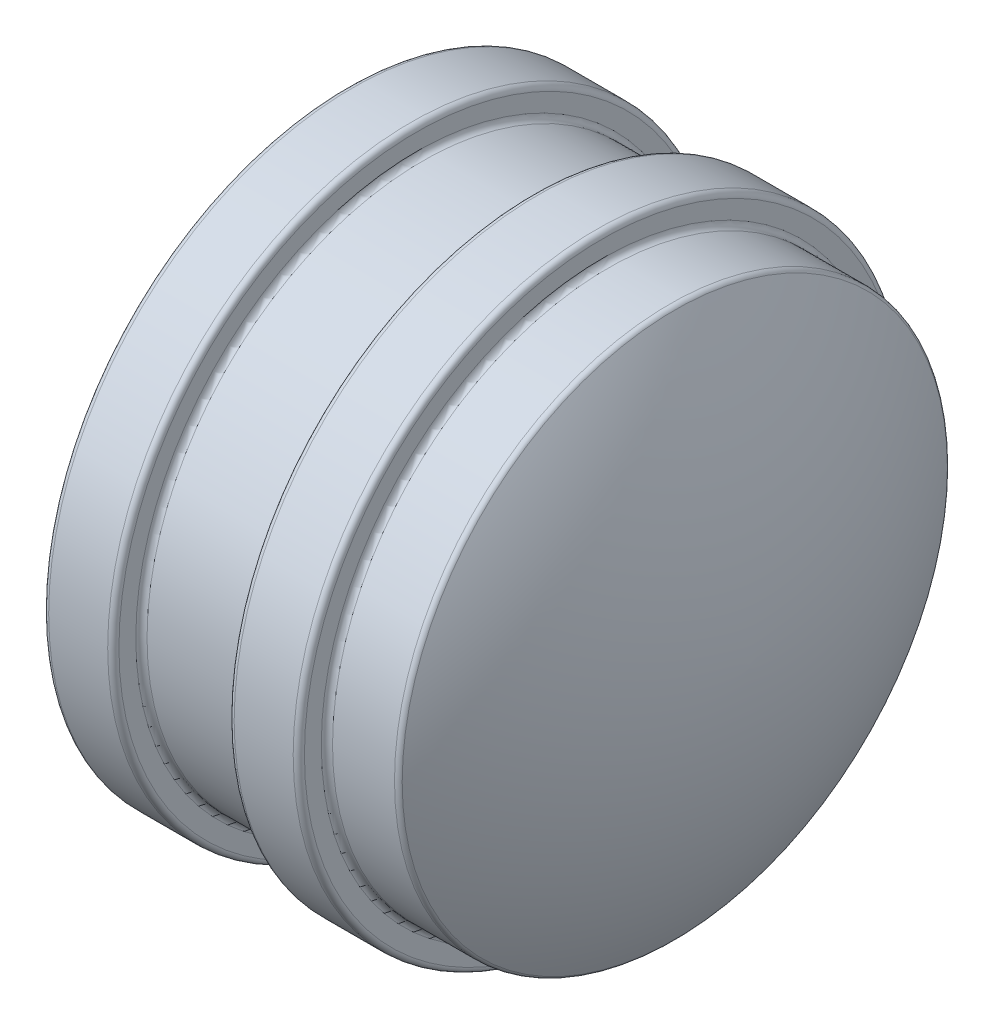
SolidWorks part; units mm, degrees
material "ABS"
ref_plane "Front Plane" through (0, 0, 0) normal (0, 0, 1) x (1, 0, 0)
ref_plane "Top Plane" through (0, 0, 0) normal (0, 1, 0) x (1, 0, 0)
ref_plane "Right Plane" through (0, 0, 0) normal (1, 0, 0) x (0, 0, -1)
sketch "Sketch2" plane through (0, 0, 0) normal (0, 0, 1) x (1, 0, 0)
  line L0 (0, 0) -> (18.1864, 0)
  line L1 (55, 0) -> (-55, 0) construction
  line L2 (14.7574, 0) -> (14.7574, 12.446) construction
  line L3 (14.7574, 12.446) -> (11.557, 12.446)
  line L4 (11.557, 12.446) -> (11.557, 13.716)
  line L5 (11.557, 13.716) -> (8.382, 13.716)
  line L6 (8.382, 13.716) -> (8.382, 12.446)
  line L7 (8.382, 12.446) -> (3.175, 12.446)
  line L8 (3.175, 12.446) -> (3.175, 13.716)
  line L9 (3.175, 13.716) -> (0, 13.716)
  line L10 (0, -55) -> (0, 55) construction
  line L11 (0, 13.716) -> (0, 0)
  arc A0 (14.7574, 12.446) -> (18.1864, 0) centre (-7.2118, -0.3021) cw
  dimension "D7" = 25.4
  dimension "D1" = 5.207
  dimension "D2" = 3.2004
  dimension "D3" = 12.446
  dimension "D4" = 1.27
  dimension "D5" = 18.1864
  dimension "D6" = 3.175
revolve "Revolve1" add sketch "Sketch2" angle 360 about L0
fillet "Fillet1" radius 0.254 8 edges at (14.7574, 0, 12.446) (11.557, 0, 12.446) (11.557, 0, 13.716) (8.382, 0, 13.716) (8.382, 0, 12.446) (3.175, 0, 12.446) (3.175, 0, 13.716) (0, 0, 13.716)
sketch "Sketch3" plane through (0, 0, 0) normal (-1, 0, 0) x (0, 0, 1)
  line L0 (-5.0289, 5.0289) -> (-5.0289, -5.0289) construction
  line L1 (0, 7.112) -> (0, -7.112) construction
  line L2 (5.0289, 5.0289) -> (5.0289, -5.0289) construction
  line L3 (-5.0289, 5.0289) -> (5.0289, 5.0289) construction
  line L4 (-7.112, 0) -> (7.112, 0) construction
  line L5 (-5.0289, -5.0289) -> (5.0289, -5.0289) construction
  circle A0 centre (0, 0) radius 2.54
  circle A1 centre (0, 7.112) radius 2.286
  circle A2 centre (5.0289, 5.0289) radius 2.286
  circle A3 centre (7.112, 0) radius 2.286
  circle A4 centre (5.0289, -5.0289) radius 2.286
  circle A5 centre (0, -7.112) radius 2.286
  circle A6 centre (-5.0289, -5.0289) radius 2.286
  circle A7 centre (-7.112, 0) radius 2.286
  circle A8 centre (-5.0289, 5.0289) radius 2.286
  dimension "D1" = 5.08
  dimension "D2" = 4.572
  dimension "D3" = 7.112
  dimension "D5" = 45
  dimension "D4" = 8
extrude "Cut-Extrude1" cut sketch "Sketch3" against normal blind 6.35
fillet "Fillet2" radius 1.27 9 edges at (6.35, -7.112, 2.286) (6.35, -5.0289, 7.3149) (6.35, 0, 9.398) (6.35, 5.0289, 7.3149) (6.35, 0, 2.54) (6.35, -5.0289, -2.7429) (6.35, 0, -4.826) (6.35, 7.112, 2.286) (6.35, 5.0289, -2.7429)
fillet "Fillet3" radius 0.254 9 edges at (0, -7.112, 2.286) (0, -5.0289, -2.7429) (0, 0, -4.826) (0, 0, 2.54) (0, -5.0289, 7.3149) (0, 0, 9.398) (0, 5.0289, 7.3149) (0, 7.112, 2.286) (0, 5.0289, -2.7429)
